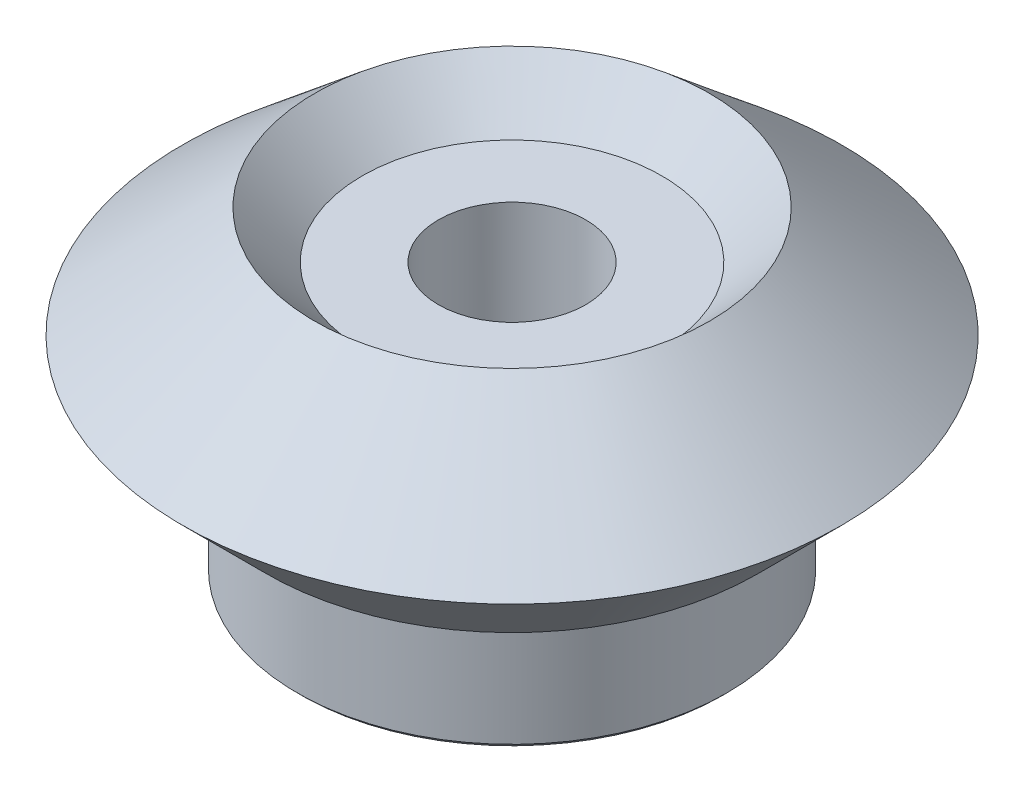
SolidWorks part; units mm, degrees
ref_plane "Front Plane" through (0, 0, 0) normal (0, 0, 1) x (1, 0, 0)
ref_plane "Top Plane" through (0, 0, 0) normal (0, 1, 0) x (1, 0, 0)
ref_plane "Right Plane" through (0, 0, 0) normal (1, 0, 0) x (0, 0, -1)
ref_plane "Plane1" through (0, 0, 40) normal (0, 0, 1) x (1, 0, 0)
sketch "Sketch1" plane through (0, 0, 40) normal (0, 0, 1) x (1, 0, 0)
  line L0 (5.3536, 0) -> (17.1464, 0)
  line L1 (17.1464, 0) -> (17.5, 0.3536)
  line L2 (17.5, 0.3536) -> (17.5, 10)
  line L3 (17.5, 10) -> (19.995, 10)
  line L4 (19.995, 10) -> (26.855, 16.86)
  line L5 (26.855, 16.86) -> (16.0855, 25.88)
  line L6 (16.0855, 25.88) -> (12.2055, 22)
  line L7 (12.2055, 22) -> (5, 22)
  line L8 (5, 22) -> (5, 0.3536)
  line L9 (5, 0.3536) -> (5.3536, 0)
  line L10 (0, 25.88) -> (0, 0) construction
  dimension "D1" = 5
  dimension "D2" = 11.7929
  dimension "D3" = 50.052
  dimension "D4" = 22
  dimension "D5" = 14.995
  dimension "D6" = 2.495
  dimension "D7" = 7.2055
  dimension "D8" = 135
  dimension "D9" = 9.6464
revolve "Revolve1" add sketch "Sketch1" angle 360 about L10
sketch "Sketch2" plane through (0, 0, 0) normal (0, -1, 0) x (1, 0, 0)
  circle A0 centre (0, 40) radius 6
  dimension "D1" = 12
extrude "Cut-Extrude1" cut sketch "Sketch2" against normal through all
